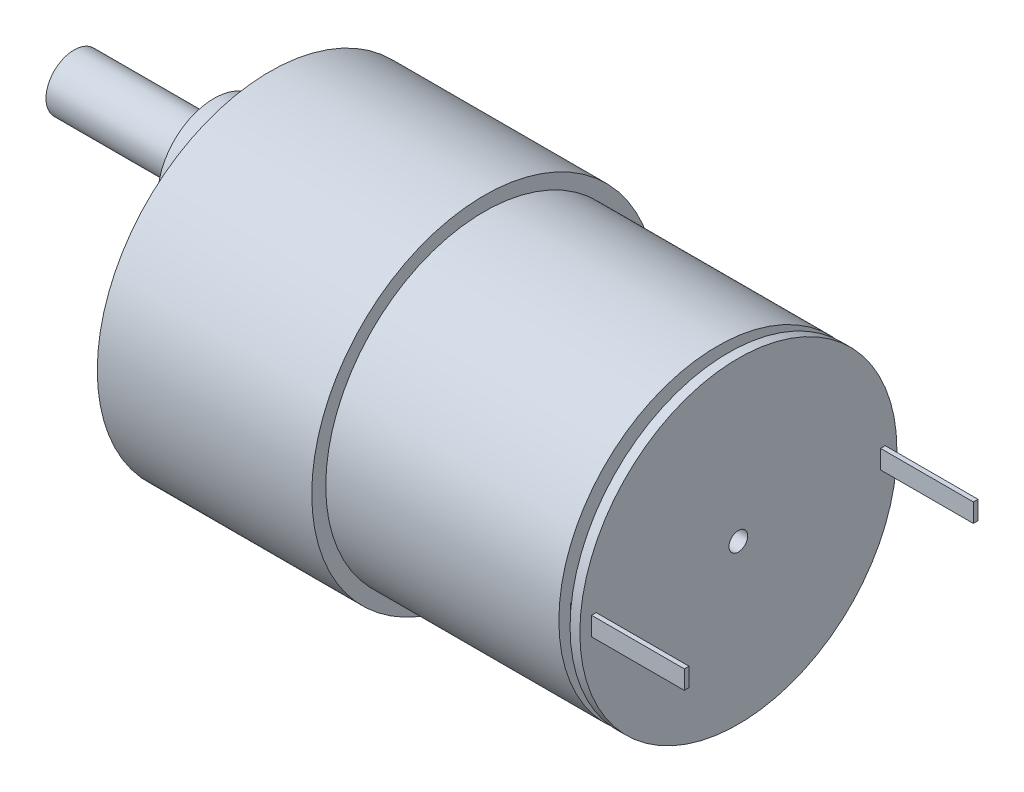
SolidWorks part; units mm, degrees
ref_plane "Front Plane" through (0, 0, 0) normal (0, 0, 1) x (1, 0, 0)
ref_plane "Top Plane" through (0, 0, 0) normal (0, 1, 0) x (1, 0, 0)
ref_plane "Right Plane" through (0, 0, 0) normal (1, 0, 0) x (0, 0, -1)
ref_plane "Plane1" through (41.25, 0, 0) normal (1, 0, 0) x (0, 0, -1)
sketch "Sketch1" plane through (41.25, 0, 0) normal (1, 0, 0) x (0, 0, -1)
  circle A0 centre (0, 0) radius 17
  dimension "D1" = 34
extrude "Boss-Extrude1" add sketch "Sketch1" against normal blind 1.05
sketch "Sketch2" plane through (40.2, 0, 0) normal (-1, 0, 0) x (0, 0, 1)
  line L0 (15.75, 1) -> (15.75, -1)
  line L1 (15.75, -1) -> (15.25, -1)
  line L2 (15.25, -1) -> (15.25, 1)
  line L3 (15.25, 1) -> (15.75, 1)
  line L4 (15.75, 1) -> (15.25, -1) construction
  line L5 (15.25, 1) -> (15.75, -1) construction
  line L6 (-15.25, 1) -> (-15.25, -1)
  line L7 (-15.25, -1) -> (-15.75, -1)
  line L8 (-15.75, -1) -> (-15.75, 1)
  line L9 (-15.75, 1) -> (-15.25, 1)
  line L10 (-15.25, 1) -> (-15.75, -1) construction
  line L11 (-15.75, 1) -> (-15.25, -1) construction
  circle A0 centre (0, 0) radius 15.5 construction
  point P7 (15.5, 0)
  point P12 (-15.5, 0)
  dimension "D3" = 31
  dimension "D1" = 2
  dimension "D2" = 0.5
extrude "Poles" add sketch "Sketch2" along normal blind 1.2 and the other way blind 11
sketch "Sketch3" plane through (40.2, 0, 0) normal (-1, 0, 0) x (0, 0, 1)
  circle A0 centre (0, 0) radius 1.5
extrude "Boss-Extrude3" add sketch "Sketch3" along normal blind 1.2
ref_plane "Plane2" through (39, 0, 0) normal (1, 0, 0) x (0, 0, -1)
sketch "Sketch5" plane through (39, 0, 0) normal (1, 0, 0) x (0, 0, -1)
  circle A2 centre (0, 0) radius 17
  dimension "D1" = 34
extrude "Boss-Extrude5" add sketch "Sketch5" against normal blind 25
ref_plane "Plane3" through (19, 0, 0) normal (1, 0, 0) x (0, 0, -1)
sketch "Sketch6" plane through (14, 0, 0) normal (1, 0, 0) x (0, 0, -1)
  circle A0 centre (0, 0) radius 18.5
  dimension "D1" = 37
extrude "Reductur" add sketch "Sketch6" against normal blind 21.5
sketch "Sketch35" plane through (-7.5, 0, 0) normal (-1, 0, 0) x (0, 0, 1)
  circle A0 centre (0, 0) radius 18.5
  circle A1 centre (0, 0) radius 18.5 construction
extrude "Endplate" add sketch "Sketch35" along normal blind 1.5
sketch "Sketch36" plane through (-9, 0, 0) normal (-1, 0, 0) x (0, 0, 1)
  circle A0 centre (0, 7) radius 6
  dimension "D2" = 12
  dimension "D1" = 7
extrude "Boss-Extrude25" add sketch "Sketch36" along normal blind 6
hole_wizard "Ø3.1 (3.1) Diameter Hole1" positions "Sketch38" profile "Sketch37" hole size "Ø3.1" standard "ANSI Metric"
sketch "Sketch38" plane through (-15, 0, 0) normal (-1, 0, 0) x (0, 0, 1)
  point P0 (0, 7)
sketch "Sketch37" plane through (-15, 7, 0) normal (0, 1, 0) x (0, 0, 1)
  line L0 (0, 0) -> (0, 2.2)
  line L1 (0, 2.2) -> (3, 2.2)
  line L2 (3, 2.2) -> (3, 0)
  line L5 (3, 0) -> (0, 0)
  line L10 (0, 2.2) -> (-3, 2.2) construction
  line L11 (0, -6.35) -> (0, 107.95) construction
  dimension "Hole Dia." = 6
  dimension "Hole Depth" = 2.2
  dimension "Drill Angle" = 180
hole_wizard "Ø2.0 (2) Diameter Hole1" positions "Sketch57" profile "Sketch56" hole size "Ø2.0" standard "ANSI Metric"
sketch "Sketch57" plane through (41.25, 0, 0) normal (1, 0, 0) x (0, 0, -1)
  point P0 (0, 0)
sketch "Sketch56" plane through (41.25, 0, 0) normal (0, 1, 0) x (0, 0, -1)
  line L0 (0, 0) -> (0, 2.25)
  line L1 (0, 2.25) -> (1, 2.25)
  line L2 (1, 2.25) -> (1, 0)
  line L5 (1, 0) -> (0, 0)
  line L10 (0, 2.25) -> (-1, 2.25) construction
  line L11 (0, -6.35) -> (0, 107.95) construction
  dimension "Hole Dia." = 2
  dimension "Hole Depth" = 2.25
  dimension "Drill Angle" = 180
ref_plane "Plane4" through (0, 0, 0) normal (0, 0, -1) x (-1, 0, 0)
sketch "Sketch39" [suppressed] plane through (-10, 0, 0) normal (-1, 0, 0) x (0, 0, 1)
  circle A0 centre (0, 7) radius 3
  dimension "D1" = 6
extrude "Shaft" [suppressed] add sketch "Sketch39" along normal blind 15
sketch "Sketch61" [suppressed] plane through (-25, 0, 0) normal (-1, 0, 0) x (0, 0, 1)
  line L4 (0, 4) -> (0, 9.4) construction
  line L5 (3, 9.4) -> (-3, 9.4)
  line L6 (-3, 9.4) -> (-3, 10)
  line L7 (-3, 10) -> (3, 10)
  line L8 (3, 10) -> (3, 9.4)
  circle A3 centre (0, 7) radius 3 construction
  point P7 (0, 9.4)
  dimension "D1" = 5.4
extrude "Flange" [suppressed] cut sketch "Sketch61" against normal blind 12
sketch "Mounting holes" plane through (-9, 0, 0) normal (-1, 0, 0) x (0, 0, 1)
  line L0 (-34.0879, 0) -> (34.0879, 0) construction
  line L1 (0, -11.3537) -> (0, 11.3537) construction
  line L2 (-13.4234, 7.75) -> (0, 0) construction
  line L3 (13.4234, 7.75) -> (0, 0) construction
  line L4 (0, -15.5) -> (0, 0) construction
  circle A0 centre (0, 0) radius 15.5 construction
  point P3 (-13.4234, 7.75)
  point P5 (0, 0)
  point P8 (-15.5, 0)
  point P11 (-7.75, 13.4234)
  point P15 (13.4234, 7.75)
  point P16 (7.75, 13.4234)
  point P18 (15.5, 0)
  point P19 (0, -15.5)
  point P20 (7.75, -13.4234)
  point P22 (-7.75, -13.4234)
  point P23 (0, 0)
  dimension "D1" = 31
  dimension "D2" = 3
hole_wizard "Ø3.0mm 定位孔1" positions "3DSketch1" profile "Sketch64" hole size "Ø3.0" standard "ISO"
sketch3d "3DSketch1"
  circle A0 centre (-9, 0, 0) radius 15.5 construction
  point P0 (-9, 0, -15.5)
  point P6 (-9, 13.4234, -7.75)
  point P9 (-9, 13.2729, 8.0051)
  point P13 (-24.5, 0, 0)
  point P17 (-9, 0, 15.5)
  point P23 (-9, -13.4234, 7.75)
  point P26 (-9, -13.4234, -7.75)
sketch "Sketch64" plane through (-9, 0, -15.5) normal (0, 1, 0) x (0, 0, 1)
  line L0 (0, 0) -> (0, 8.4013)
  line L1 (0, 8.4013) -> (1.5, 7.5)
  line L2 (1.5, 7.5) -> (1.5, 0)
  line L5 (1.5, 0) -> (0, 0)
  line L10 (0, 8.4013) -> (-1.5, 7.5) construction
  line L11 (0, -6.35) -> (0, 107.95) construction
  dimension "Hole Dia." = 3
  dimension "Hole Depth" = 7.5
  dimension "Drill Angle" = 118
split "Split1" [suppressed] bodies to split 160 161
sketch "草圖1" plane through (-9, 0, 0) normal (-1, 0, 0) x (0, 0, 1)
  circle A0 centre (0, 7) radius 3
extrude "填料-伸長1" add sketch "草圖1" along normal blind 21
